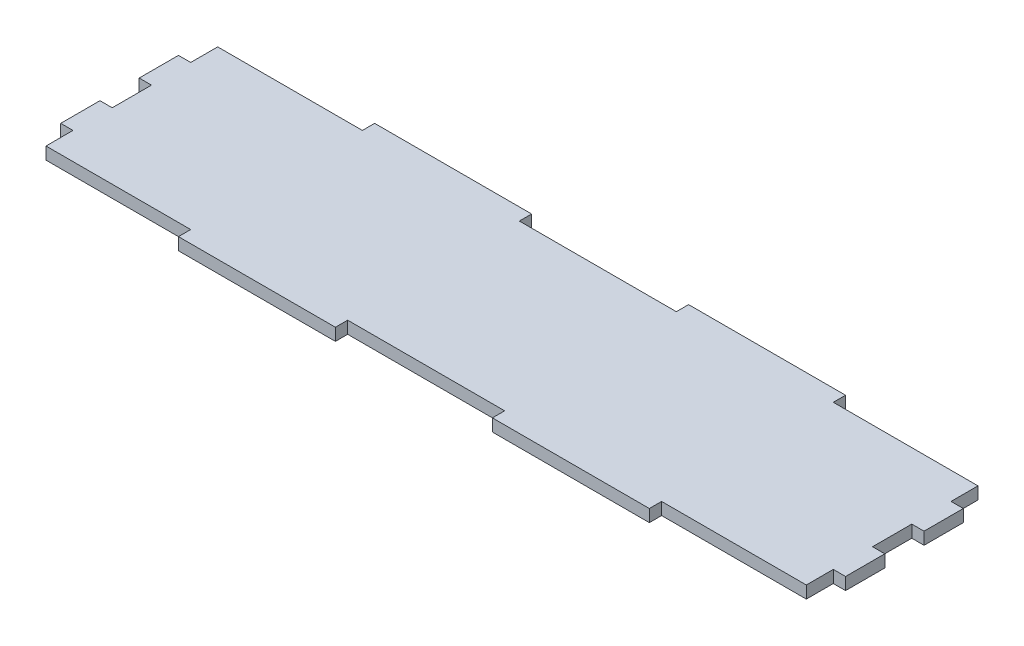
SolidWorks part; units mm, degrees
ref_plane "Front Plane" through (0, 0, 0) normal (0, 0, 1) x (1, 0, 0)
ref_plane "Top Plane" through (0, 0, 0) normal (0, 1, 0) x (1, 0, 0)
ref_plane "Right Plane" through (0, 0, 0) normal (1, 0, 0) x (0, 0, -1)
sketch "Sketch1" plane through (0, 0, 0) normal (0, 1, 0) x (1, 0, 0)
  line L1 (-101.6, -25.4) -> (101.6, -25.4)
  line L2 (-101.6, -25.4) -> (-101.6, 25.4)
  line L3 (-101.6, 25.4) -> (101.6, 25.4)
  line L4 (101.6, -25.4) -> (101.6, 25.4)
  line L5 (-101.6, -25.4) -> (101.6, 25.4) construction
  line L6 (-101.6, 25.4) -> (101.6, -25.4) construction
  point P0 (0, 0)
  dimension "D1" = 203.2
  dimension "D2" = 50.8
extrude "Boss-Extrude1" add sketch "Sketch1" along normal blind 3.175
sketch "Sketch2" plane through (0, 3.175, 0) normal (0, 1, 0) x (1, 0, 0)
  line L1 (-101.6, 25.4) -> (-60.96, 25.4)
  line L2 (-101.6, 25.4) -> (-101.6, 22.225)
  line L3 (-101.6, 22.225) -> (-60.96, 22.225)
  line L4 (-60.96, 25.4) -> (-60.96, 22.225)
  line L5 (-101.6, -25.4) -> (-60.96, -25.4)
  line L6 (-101.6, -25.4) -> (-101.6, -22.225)
  line L7 (-101.6, -22.225) -> (-60.96, -22.225)
  line L8 (-60.96, -25.4) -> (-60.96, -22.225)
  dimension "D1" = 40.64
  dimension "D2" = 3.175
  dimension "D3" = 3.175
extrude "Cut-Extrude2" cut sketch "Sketch2" against normal blind 3.175
pattern_linear "LPattern1" count 3 spacing 81.28 along (1, 0, 0) of "Cut-Extrude2"
sketch "Sketch3" plane through (0, 3.175, 0) normal (0, 1, 0) x (1, 0, 0)
  line L0 (-101.6, 18.9382) -> (-101.6, 44.3303) construction
  line L2 (101.6, 11.0748) -> (101.6, 37.7775) construction
  line L3 (-101.6, 5.08) -> (-98.425, 5.08)
  line L4 (-29.7493, 25.4) -> (26.9325, 25.4) construction
  line L5 (-101.6, 5.08) -> (-101.6, -5.08)
  line L6 (-101.6, -5.08) -> (-98.425, -5.08)
  line L7 (-98.425, 5.08) -> (-98.425, -5.08)
  line L8 (-28.1111, -25.4) -> (26.9325, -25.4) construction
  line L9 (101.6, -5.08) -> (98.425, -5.08)
  line L10 (101.6, -5.08) -> (101.6, 5.08)
  line L11 (101.6, 5.08) -> (98.425, 5.08)
  line L12 (98.425, -5.08) -> (98.425, 5.08)
  dimension "D1" = 10.16
  dimension "D2" = 3.175
  dimension "D3" = 20.32
  dimension "D4" = 3.175
extrude "Cut-Extrude3" cut sketch "Sketch3" against normal blind 3.175
pattern_linear "LPattern2" count 2 spacing 20.32 along (0, 0, 1) of "Cut-Extrude3"
pattern_linear "LPattern3" count 2 spacing 20.32 along (0, 0, -1) of "Cut-Extrude3"
